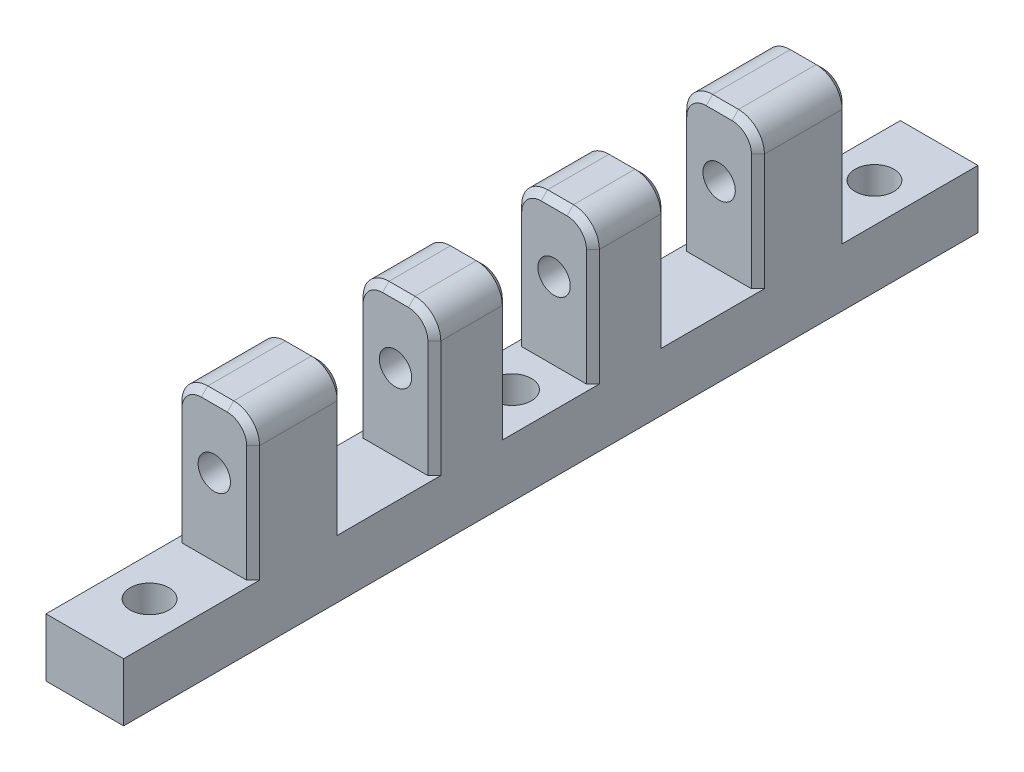
SolidWorks part; units mm, degrees
ref_plane "前视基准面" through (0, 0, 0) normal (0, 0, 1) x (1, 0, 0)
ref_plane "上视基准面" through (0, 0, 0) normal (0, 1, 0) x (1, 0, 0)
ref_plane "右视基准面" through (0, 0, 0) normal (1, 0, 0) x (0, 0, -1)
sketch "草图1" plane through (0, 0, 0) normal (1, 0, 0) x (0, 0, -1)
  line L1 (33, 2.25) -> (-33, 2.25)
  line L2 (33, 2.25) -> (33, -2.25)
  line L3 (33, -2.25) -> (-33, -2.25)
  line L4 (-33, 2.25) -> (-33, -2.25)
  line L5 (33, 2.25) -> (-33, -2.25) construction
  line L6 (33, -2.25) -> (-33, 2.25) construction
  point P0 (0, 0)
extrude "凸台-拉伸1" add sketch "草图1" along normal blind 6
sketch "草图2" plane through (0, 0, 0) normal (-1, 0, 0) x (0, 0, 1)
  line L0 (0, 14.9379) -> (0, -18.8025) construction
  line L1 (0, 0) -> (6.125, 0) construction
  line L2 (0, 5.2248) -> (19.5, 5.2248) construction
  line L3 (6.125, 0) -> (6.125, 20.9022) construction
  line L4 (19.5, 5.2248) -> (19.5, 20.9022) construction
  line L5 (6.125, 12.041) -> (9, 12.041) construction
  line L6 (19.5, 10.9334) -> (23, 10.9334) construction
  line L7 (9, 2.25) -> (9, 13.25)
  line L8 (-33, 2.25) -> (33, 2.25) construction
  line L9 (3.25, 13.25) -> (9, 13.25)
  line L10 (23, 2.25) -> (23, 13.25)
  line L11 (-23, 2.25) -> (-23, 13.25)
  line L12 (3.25, 2.25) -> (3.25, 13.25)
  line L13 (16, 2.25) -> (16, 13.25)
  line L14 (-16, 13.25) -> (-23, 13.25)
  line L15 (16, 13.25) -> (23, 13.25)
  line L16 (-16, 2.25) -> (-16, 13.25)
  line L17 (-9, 2.25) -> (-9, 13.25)
  line L18 (-3.25, 2.25) -> (-3.25, 13.25)
  line L19 (-3.25, 13.25) -> (-9, 13.25)
  line L20 (-23, 2.25) -> (-16, 2.25)
  line L21 (-9, 2.25) -> (-3.25, 2.25)
  line L22 (3.25, 2.25) -> (9, 2.25)
  line L23 (16, 2.25) -> (23, 2.25)
  point P22 (6.125, 13.25)
extrude "凸台-拉伸2" add sketch "草图2" against normal blind 6
sketch "草图3" plane through (0, 0, 23) normal (0, 0, 1) x (1, 0, 0)
  line L0 (3, 17.3421) -> (3, -6.5139) construction
  line L1 (3, -2.25) -> (3, 8.182) construction
  line L2 (6, -2.25) -> (0, -2.25) construction
  circle A0 centre (3, 8.182) radius 1.25
extrude "切除-拉伸1" cut sketch "草图3" against normal blind 51
sketch "草图4" plane through (0, 2.25, 0) normal (0, 1, 0) x (1, 0, 0)
  line L0 (0, 0) -> (23.9499, 0) construction
  line L1 (0, 12.5) -> (33.42, 12.5) construction
  line L2 (0, 16) -> (0, 9) construction
  line L3 (0, -12.5) -> (39.0219, -12.5) construction
  line L4 (0, -9) -> (0, -16) construction
  line L5 (3, 33) -> (3, -33) construction
  line L6 (6, 33) -> (0, 33) construction
  line L7 (6, -33) -> (0, -33) construction
  line L8 (3, 0) -> (3, 28) construction
  circle A0 centre (3, 0) radius 1.5
  circle A1 centre (3, 28) radius 1.5
  circle A2 centre (3, -28) radius 1.5
extrude "切除-拉伸2" cut sketch "草图4" against normal blind 51
fillet "圆角1" radius 2 1 edges at (6, 13.25, 19.5)
fillet "圆角2" radius 2 1 edges at (6, 13.25, -19.5)
fillet "圆角3" radius 2 2 edges at (6, 13.25, 6.125)
fillet "圆角4" radius 2 1 edges at (6, 13.25, -6.125)
fillet "圆角5" radius 2 1 edges at (0, 13.25, -19.5)
fillet "圆角6" radius 2 1 edges at (0, 13.25, -6.125)
fillet "圆角7" radius 2 2 edges at (0, 13.25, 6.125)
fillet "圆角8" radius 2 1 edges at (0, 13.25, 19.5)
chamfer "倒角1" distance 0.5 angle 45 5 edges at (0, 6.75, -16) (6, 6.75, -16) (0.5858, 12.6642, -16) (5.4142, 12.6642, -16) (3, 13.25, -16)
chamfer "倒角2" distance 0.5 angle 45 35 edges at (0, 6.75, -23) (6, 6.75, -23) (0.5858, 12.6642, -23) (5.4142, 12.6642, -23) (3, 13.25, -23) (0, 6.75, -9) (6, 6.75, -9) (0.5858, 12.6642, -9) (5.4142, 12.6642, -9) (3, 13.25, -9) (0.5858, 12.6642, 3.25) (5.4142, 12.6642, 3.25) (3, 13.25, 3.25) (0, 6.75, 16) (6, 6.75, 16) (0.5858, 12.6642, 16) (5.4142, 12.6642, 16) (3, 13.25, 16) (0, 6.75, 23) (6, 6.75, 23) (0.5858, 12.6642, 23) (5.4142, 12.6642, 23) (3, 13.25, 23) (0.5858, 12.6642, 9) (5.4142, 12.6642, 9) (3, 13.25, 9) (0, 6.75, -3.25) (6, 6.75, -3.25) (0.5858, 12.6642, -3.25) (5.4142, 12.6642, -3.25) (3, 13.25, -3.25)
